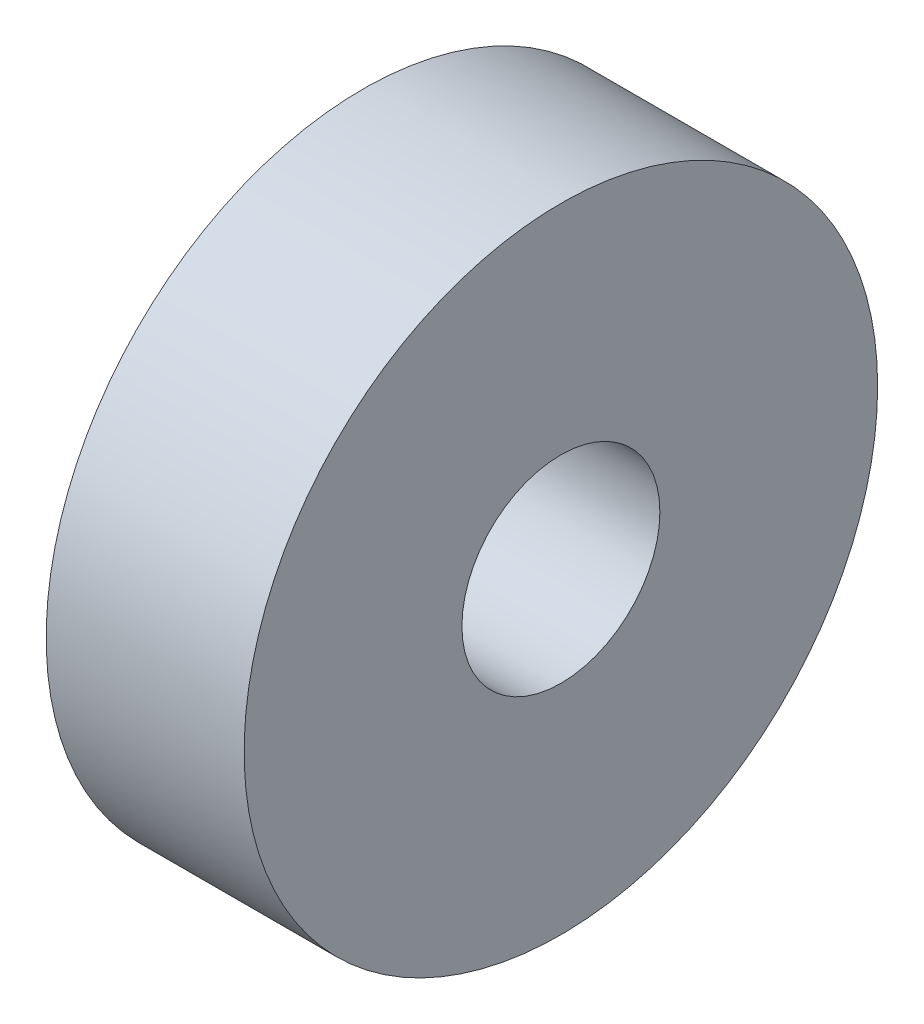
SolidWorks part; units mm, degrees
ref_plane "Front Plane" through (0, 0, 0) normal (0, 0, 1) x (1, 0, 0)
ref_plane "Top Plane" through (0, 0, 0) normal (0, 1, 0) x (1, 0, 0)
ref_plane "Right Plane" through (0, 0, 0) normal (1, 0, 0) x (0, 0, -1)
sketch "Sketch1" plane through (0, 0, 0) normal (1, 0, 0) x (0, 0, -1)
  circle A0 centre (0, 0) radius 8
  circle A1 centre (0, 0) radius 2.5
  dimension "D1" = 16
  dimension "D2" = 5
extrude "Boss-Extrude1" add sketch "Sketch1" along normal blind 5
